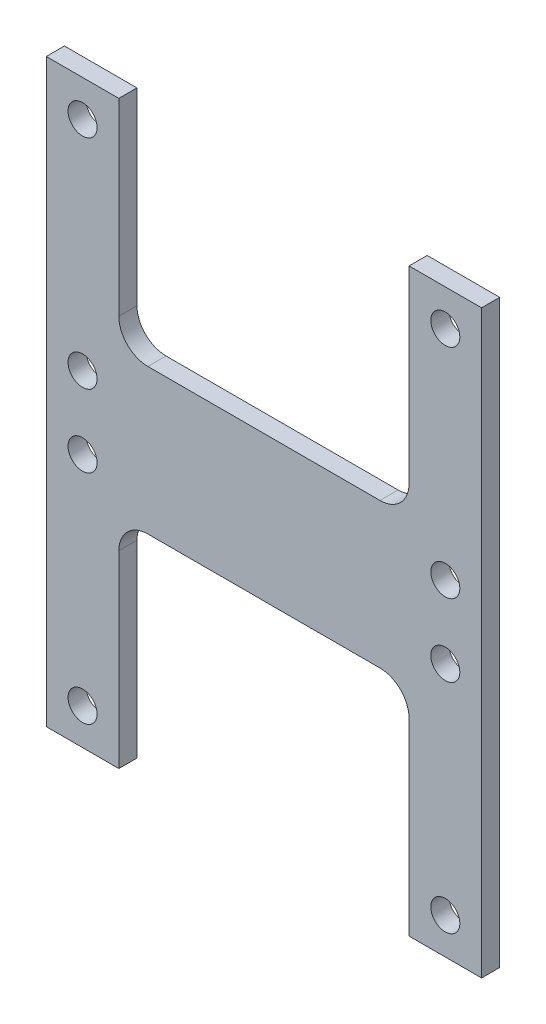
SolidWorks part; units mm, degrees
material "Acrylic (Medium-high impact)"
ref_plane "Front Plane" through (0, 0, 0) normal (0, 0, 1) x (1, 0, 0)
ref_plane "Top Plane" through (0, 0, 0) normal (0, 1, 0) x (1, 0, 0)
ref_plane "Right Plane" through (0, 0, 0) normal (1, 0, 0) x (0, 0, -1)
sketch "Sketch1" plane through (0, 0, 0) normal (0, 0, 1) x (1, 0, 0)
  line L0 (-38.1, 0) -> (38.1, 0)
  line L1 (-38.1, 50.8) -> (-25.4, 50.8)
  line L2 (-38.1, 50.8) -> (-38.1, -50.8)
  line L3 (-38.1, -50.8) -> (-25.4, -50.8)
  line L4 (38.1, 50.8) -> (38.1, -50.8)
  line L5 (-38.1, 50.8) -> (38.1, -50.8) construction
  line L6 (-38.1, -50.8) -> (38.1, 50.8) construction
  line L7 (-25.4, 50.8) -> (-25.4, 12.7)
  line L8 (-25.4, 12.7) -> (25.4, 12.7)
  line L9 (25.4, 12.7) -> (25.4, 50.8)
  line L10 (25.4, 50.8) -> (38.1, 50.8)
  line L11 (25.4, 12.7) -> (25.4, 0) construction
  line L12 (-25.4, -50.8) -> (-25.4, -12.7)
  line L13 (-25.4, -12.7) -> (25.4, -12.7)
  line L14 (25.4, -12.7) -> (25.4, -50.8)
  line L15 (25.4, -50.8) -> (38.1, -50.8)
  point P0 (0, 0)
  dimension "D1" = 76.2
  dimension "D2" = 101.6
  dimension "D3" = 12.7
extrude "Boss-Extrude1" add sketch "Sketch1" along normal blind 3.175 contours L4 L1 L2 L0 | L4 L0 L2 L3
sketch "Sketch4" plane through (0, 0, 3.175) normal (0, 0, 1) x (1, 0, 0)
  line L0 (-31.75, 44.45) -> (-31.75, 6.35) construction
  line L1 (-31.75, 6.35) -> (31.75, 6.35) construction
  line L2 (31.75, 6.35) -> (31.75, 44.45) construction
  line L3 (31.75, 44.45) -> (-31.75, 44.45) construction
  line L4 (31.75, 44.45) -> (31.75, 50.8) construction
  line L5 (25.4, 50.8) -> (38.1, 50.8) construction
  line L6 (0, 6.35) -> (0, 0) construction
  line L7 (-38.1, 0) -> (38.1, 0) construction
  line L8 (-38.1, 50.8) -> (-38.1, -50.8) construction
  line L9 (38.1, 50.8) -> (38.1, -50.8) construction
  circle A0 centre (-31.75, 44.45) radius 2.54
  circle A1 centre (-31.75, 6.35) radius 2.54
  circle A2 centre (31.75, 6.35) radius 2.54
  circle A3 centre (31.75, 44.45) radius 2.54
  circle A4 centre (-31.75, -6.35) radius 2.54
  circle A5 centre (31.75, -6.35) radius 2.54
  circle A6 centre (31.75, -44.45) radius 2.54
  circle A7 centre (-31.75, -44.45) radius 2.54
  dimension "D1" = 5.08
  dimension "D2" = 63.5
  dimension "D3" = 38.1
extrude "Cut-Extrude3" cut sketch "Sketch4" against normal through all
fillet "Fillet1" radius 5.08 4 edges at (-25.4, -12.7, 1.5875) (25.4, -12.7, 1.5875) (25.4, 12.7, 1.5875) (-25.4, 12.7, 1.5875)
